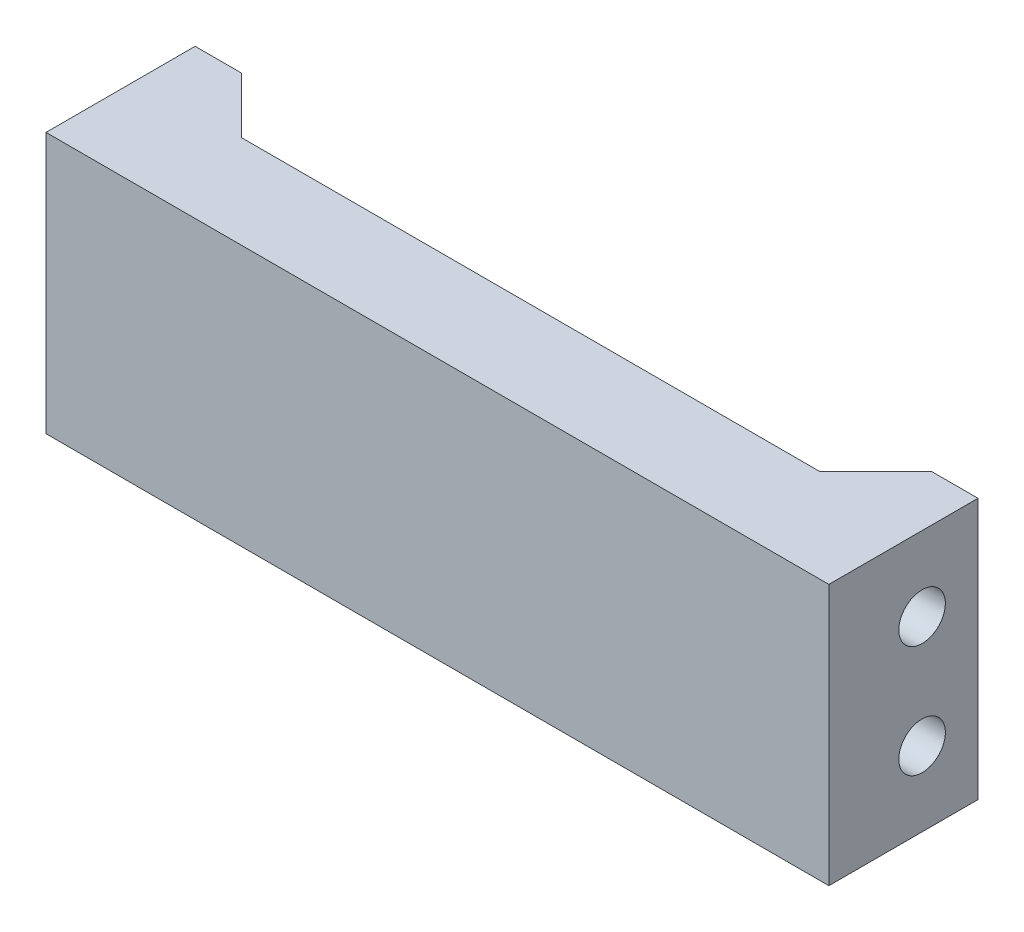
SolidWorks part; units mm, degrees
ref_plane "Front Plane" through (0, 0, 0) normal (0, 0, 1) x (1, 0, 0)
ref_plane "Top Plane" through (0, 0, 0) normal (0, 1, 0) x (1, 0, 0)
ref_plane "Right Plane" through (0, 0, 0) normal (1, 0, 0) x (0, 0, -1)
sketch "Sketch1" plane through (0, 0, 0) normal (0, 0, 1) x (1, 0, 0)
  line L1 (-21, 7) -> (21, 7)
  line L2 (-21, 7) -> (-21, -7)
  line L3 (-21, -7) -> (21, -7)
  line L4 (21, 7) -> (21, -7)
  line L5 (-21, 7) -> (21, -7) construction
  line L6 (-21, -7) -> (21, 7) construction
  point P0 (0, 0)
  dimension "D1" = 14
  dimension "D2" = 42
extrude "Boss-Extrude1" add sketch "Sketch1" along normal blind 2
sketch "Sketch2" plane through (0, 0, 0) normal (0, 0, -1) x (-1, 0, 0)
  line L0 (21, -7) -> (-21, -7) construction
  line L1 (-21, 7) -> (-18.5, 7)
  line L2 (-21, 7) -> (-21, -7)
  line L3 (-21, -7) -> (-18.5, -7)
  line L4 (-18.5, 7) -> (-18.5, -7)
  line L5 (0, 7) -> (0, -7) construction
  line L6 (-21, 7) -> (21, 7) construction
  line L7 (21, -7) -> (18.5, -7)
  line L8 (18.5, 7) -> (18.5, -7)
  line L9 (21, 7) -> (18.5, 7)
  line L10 (21, 7) -> (21, -7)
  dimension "D1" = 2.5
extrude "Boss-Extrude2" add sketch "Sketch2" along normal blind 6
sketch "Sketch5" plane through (21, 0, 0) normal (1, 0, 0) x (0, 0, -1)
  line L0 (0, 7) -> (0, -7) construction
  line L1 (-2, 7) -> (6, 7) construction
  line L2 (-2, -7) -> (6, -7) construction
  line L3 (-2, -7) -> (-2, 7) construction
  line L4 (3, 7) -> (3, -7) construction
  line L5 (6, 7) -> (6, -7) construction
  line L6 (-2, 0) -> (6, 0) construction
  circle A0 centre (3, 3) radius 1.25
  circle A1 centre (3, -3) radius 1.25
  dimension "D3" = 2.5
  dimension "D1" = 2
  dimension "D2" = 3
  dimension "D4" = 4
extrude "Cut-Extrude1" cut sketch "Sketch5" against normal through all
sketch "Sketch6" plane through (0, 7, 0) normal (0, 1, 0) x (1, 0, 0)
  line L0 (-18.5, 6) -> (-18.5, 0) construction
  line L1 (-18.5, 6) -> (-18.5, 0)
  line L2 (-18.5, 0) -> (-12.5, 0)
  line L3 (18.5, 0) -> (-18.5, 0) construction
  line L4 (-18.5, 6) -> (-15.5, 3)
  line L5 (0, 0) -> (0, -2) construction
  line L6 (21, -2) -> (-21, -2) construction
  line L7 (18.5, 6) -> (18.5, 0)
  line L8 (18.5, 0) -> (12.5, 0)
  line L9 (18.5, 6) -> (15.5, 3)
  line L10 (-15.5, 3) -> (15.5, 3)
  line L11 (-12.5, 0) -> (12.5, 0)
  dimension "D1" = 6
extrude "Boss-Extrude3" add sketch "Sketch6" against normal blind 2
mirror "Mirror1" about plane through (0, 0, 0) normal (0, 1, 0) of "Boss-Extrude3"
